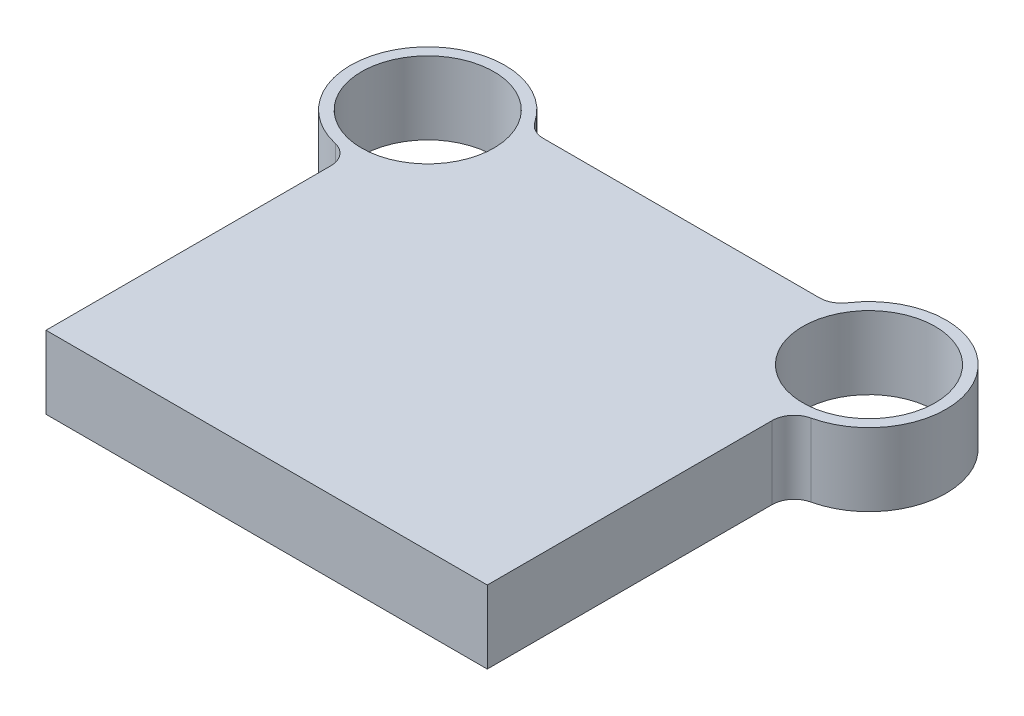
SolidWorks part; units mm, degrees
ref_plane "Front Plane" through (0, 0, 0) normal (0, 0, 1) x (1, 0, 0)
ref_plane "Top Plane" through (0, 0, 0) normal (0, 1, 0) x (1, 0, 0)
ref_plane "Right Plane" through (0, 0, 0) normal (1, 0, 0) x (0, 0, -1)
sketch "Sketch1" plane through (0, 0, 0) normal (0, 1, 0) x (1, 0, 0)
  line L0 (100, 0) -> (-100, 0)
  line L1 (-100, 0) -> (-100, 138)
  line L2 (0, 0) -> (0, 188) construction
  line L3 (68.3772, 188) -> (-68.3772, 188)
  line L4 (100, 0) -> (100, 138)
  arc A0 (-68.3772, 188) -> (-100, 138) centre (-100, 173) ccw
  circle A1 centre (-100, 173) radius 30
  arc A2 (68.3772, 188) -> (100, 138) centre (100, 173) cw
  circle A3 centre (100, 173) radius 30
  point P11 (0, 0)
  dimension "D1" = 70
  dimension "D2" = 60
  dimension "D3" = 188
  dimension "D4" = 173
  dimension "D5" = 200
  dimension "D6" = 200
extrude "Boss-Extrude1" add sketch "Sketch1" along normal blind 33
fillet "Fillet1" radius 10 4 edges at (100, 16.5, -138) (68.3772, 16.5, -188) (-68.3772, 16.5, -188) (-100, 16.5, -138)
